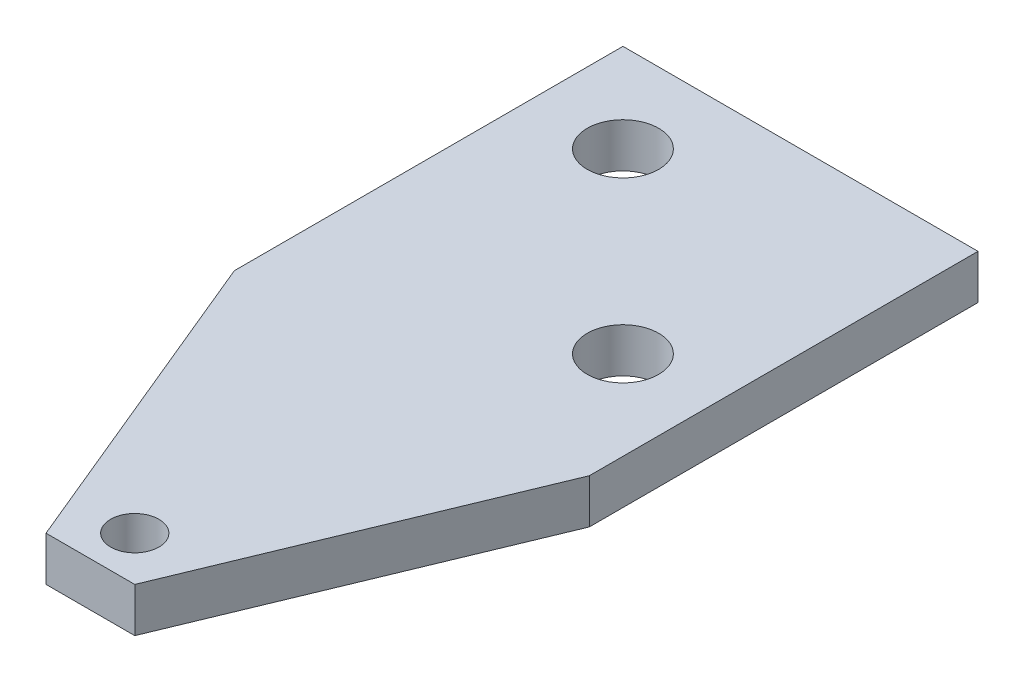
SolidWorks part; units mm, degrees
material "Copper"
ref_plane "Front Plane" through (0, 0, 0) normal (0, 0, 1) x (1, 0, 0)
ref_plane "Top Plane" through (0, 0, 0) normal (0, 1, 0) x (1, 0, 0)
ref_plane "Right Plane" through (0, 0, 0) normal (1, 0, 0) x (0, 0, -1)
sketch "Sketch1" plane through (0, 0, 0) normal (0, 1, 0) x (1, 0, 0)
  line L0 (-12.7, -12.7) -> (-12.7, -15.1046)
  line L1 (-12.7, 12.7) -> (12.7, 12.7)
  line L2 (-12.7, 12.7) -> (-12.7, -12.7)
  line L3 (-12.7, -12.7) -> (12.7, -12.7) construction
  line L4 (12.7, 12.7) -> (12.7, -12.7)
  line L5 (-12.7, 12.7) -> (12.7, -12.7) construction
  line L6 (-12.7, -12.7) -> (12.7, 12.7) construction
  line L7 (-12.7, -15.1046) -> (-3.175, -38.1)
  line L8 (-3.175, -38.1) -> (3.175, -38.1)
  line L9 (3.175, -38.1) -> (12.7, -15.1046)
  line L10 (12.7, -15.1046) -> (12.7, -12.7)
  point P0 (0, 0)
  point P6 (12.7, -30.3832)
  dimension "D1" = 25.4
  dimension "D2" = 25.4
  dimension "D3" = 6.35
  dimension "D4" = 25.4
  dimension "D5" = 22.5
extrude "Boss-Extrude1" add sketch "Sketch1" along normal blind 3.175 contours L2 L0 L7 L8 L9 L10 L4 L1
hole_wizard "#10 Clearance Hole1" positions "Sketch2" profile "Sketch3" hole size "#10" standard "ANSI Inch" end condition through all
sketch "Sketch2" plane through (0, 3.175, 0) normal (0, 1, 0) x (1, 0, 0)
  point P0 (-6.35, 6.35)
  point P2 (6.35, -6.35)
  dimension "D1" = 6.35
  dimension "D2" = 6.35
  dimension "D3" = 6.35
  dimension "D4" = 6.35
sketch "Sketch3" plane through (-6.35, 3.175, -6.35) normal (1, 0, 0) x (0, 0, 1)
  line L0 (0, 0) -> (0, 3.175)
  line L1 (0, 3.175) -> (2.5527, 3.175)
  line L2 (2.5527, 3.175) -> (2.5527, 0)
  line L5 (2.5527, 0) -> (0, 0)
  line L11 (0, -6.35) -> (0, 107.95) construction
  dimension "Thru Hole Dia." = 5.1054
  dimension "Thru Hole Depth" = 3.175
hole_wizard "#8-32 Tapped Hole1" positions "Sketch4" profile "Sketch5" tap size "#8-32" standard "ANSI Inch" end condition through all
sketch "Sketch4" plane through (0, 3.175, 0) normal (0, 1, 0) x (1, 0, 0)
  line L0 (-3.175, -38.1) -> (3.175, -38.1) construction
  point P0 (0, -34.925)
  dimension "D1" = 3.175
sketch "Sketch5" plane through (0, 3.175, 34.925) normal (1, 0, 0) x (0, 0, 1)
  line L0 (0, 0) -> (0, 3.175)
  line L1 (0, 3.175) -> (1.7272, 3.175)
  line L2 (1.7272, 3.175) -> (1.7272, 0)
  line L5 (1.7272, 0) -> (0, 0)
  line L11 (0, -6.35) -> (0, 107.95) construction
  dimension "Thru Tap Drill Dia." = 3.4544
  dimension "Thru Tap Drill Depth" = 3.175
cosmetic thread "Hole Thread1" parameters "D2"=4.1656
